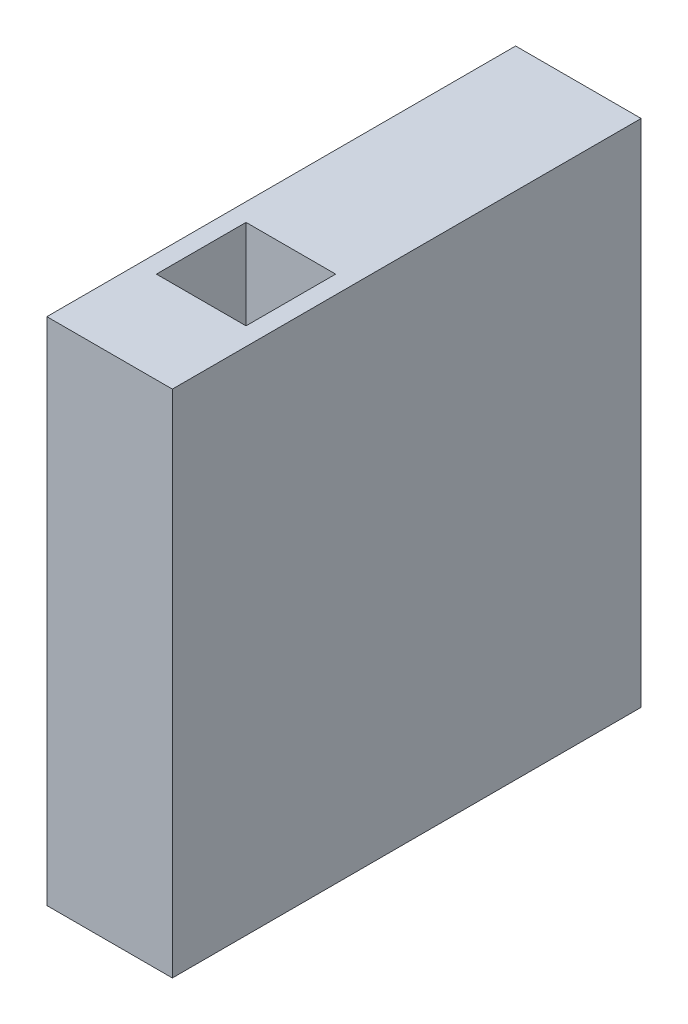
SolidWorks part; units mm, degrees
ref_plane "Спереди" through (0, 0, 0) normal (0, 0, 1) x (1, 0, 0)
ref_plane "Сверху" through (0, 0, 0) normal (0, 1, 0) x (1, 0, 0)
ref_plane "Справа" through (0, 0, 0) normal (1, 0, 0) x (0, 0, -1)
sketch "Эскиз2" plane through (0, 0, 0) normal (0, 1, 0) x (1, 0, 0)
  line L1 (-7, 26.15) -> (7, 26.15)
  line L2 (-7, 26.15) -> (-7, -26.15)
  line L3 (-7, -26.15) -> (7, -26.15)
  line L4 (7, 26.15) -> (7, -26.15)
  line L5 (-7, 26.15) -> (7, -26.15) construction
  line L6 (-7, -26.15) -> (7, 26.15) construction
  point P0 (0, 0)
extrude "Бобышка-Вытянуть1" add sketch "Эскиз2" along normal blind 56.9
sketch "Эскиз3" plane through (0, 56.9, 0) normal (0, 1, 0) x (1, 0, 0)
  line L0 (0, -26.15) -> (0, 26.15)
  line L2 (-7, -26.15) -> (7, -26.15) construction
  line L4 (7, 26.15) -> (-7, 26.15) construction
  line L5 (-7, -26.15) -> (-7, -10.93)
  line L6 (-7, 26.15) -> (-7, -26.15) construction
  line L7 (-7, -10.93) -> (7, -10.93)
  line L8 (7, -26.15) -> (7, 26.15) construction
  line L10 (-5, -5.93) -> (5, -5.93)
  line L11 (-5, -5.93) -> (-5, -15.93)
  line L12 (-5, -15.93) -> (5, -15.93)
  line L13 (5, -5.93) -> (5, -15.93)
  line L14 (-5, -5.93) -> (5, -15.93) construction
  line L15 (-5, -15.93) -> (5, -5.93) construction
  point P13 (0, -10.93)
extrude "Вырез-Вытянуть1" cut sketch "Эскиз3" against normal blind 56.9 contours L11 L12 L0 L7 | L10 L11 L7 L0 | L13 L10 L0 L7 | L13 L7 L0 L12
